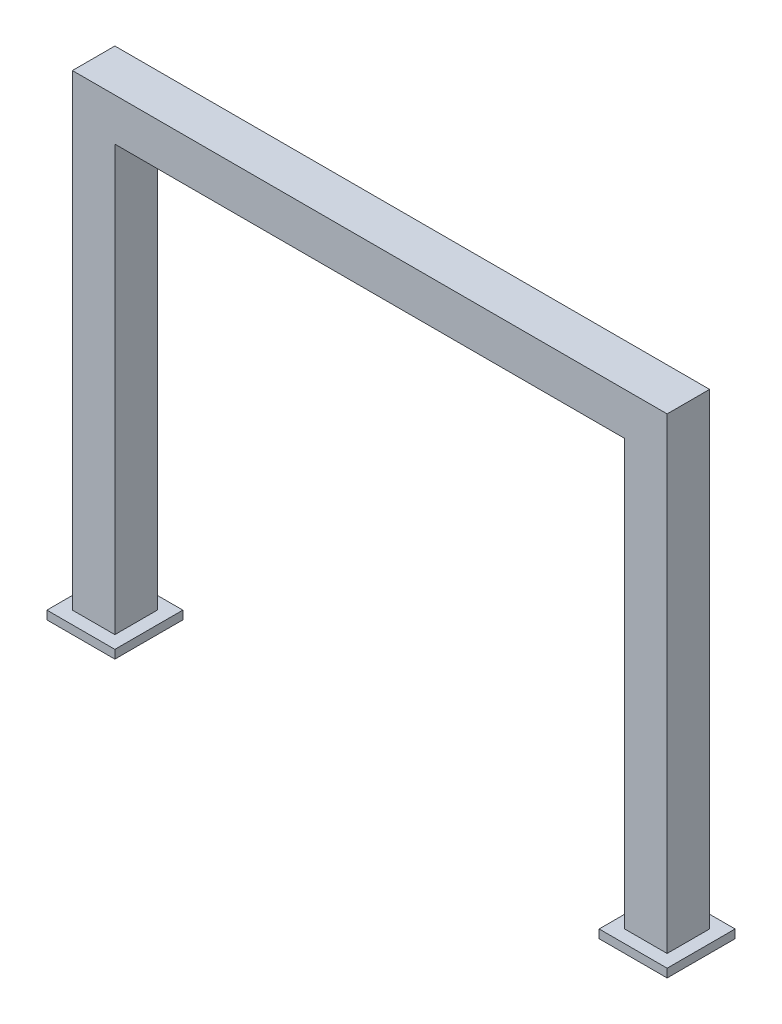
SolidWorks part; units mm, degrees
ref_plane "前视基准面" through (0, 0, 0) normal (0, 0, 1) x (1, 0, 0)
ref_plane "上视基准面" through (0, 0, 0) normal (0, 1, 0) x (1, 0, 0)
ref_plane "右视基准面" through (0, 0, 0) normal (1, 0, 0) x (0, 0, -1)
sketch "草图1" plane through (0, 0, 0) normal (0, 0, 1) x (1, 0, 0)
  line L0 (-350, 0) -> (-350, 550)
  line L1 (-350, 550) -> (350, 550)
  line L2 (350, 550) -> (350, 0)
  line L3 (350, 0) -> (300, 0)
  line L4 (300, 0) -> (300, 500)
  line L5 (300, 500) -> (-300, 500)
  line L6 (-300, 500) -> (-300, 0)
  line L7 (-300, 0) -> (-350, 0)
  line L8 (0, 0) -> (0, 68.1651) construction
  dimension "D1" = 50
  dimension "D2" = 50
  dimension "D3" = 500
  dimension "D4" = 600
  dimension "D5" = 500
extrude "凸台-拉伸1" add sketch "草图1" along normal mid plane 50
sketch "草图2" plane through (0, 0, 0) normal (0, -1, 0) x (1, 0, 0)
  line L0 (-350, 0) -> (350, 0) construction
  line L1 (-285, -40) -> (-365, -40)
  line L2 (-285, -40) -> (-285, 40)
  line L3 (-285, 40) -> (-365, 40)
  line L4 (-365, -40) -> (-365, 40)
  line L5 (-285, -40) -> (-365, 40) construction
  line L6 (-285, 40) -> (-365, -40) construction
  line L7 (365, -40) -> (285, -40)
  line L8 (365, -40) -> (365, 40)
  line L9 (365, 40) -> (285, 40)
  line L10 (285, -40) -> (285, 40)
  line L11 (365, -40) -> (285, 40) construction
  line L12 (365, 40) -> (285, -40) construction
  line L13 (-350, 25) -> (-350, -25) construction
  line L14 (350, 25) -> (350, -25) construction
  point P0 (-325, 0)
  point P5 (325, 0)
  dimension "D1" = 80
  dimension "D2" = 80
  dimension "D3" = 15
  dimension "D4" = 80
  dimension "D5" = 80
  dimension "D6" = 15
extrude "凸台-拉伸2" add sketch "草图2" along normal blind 10
